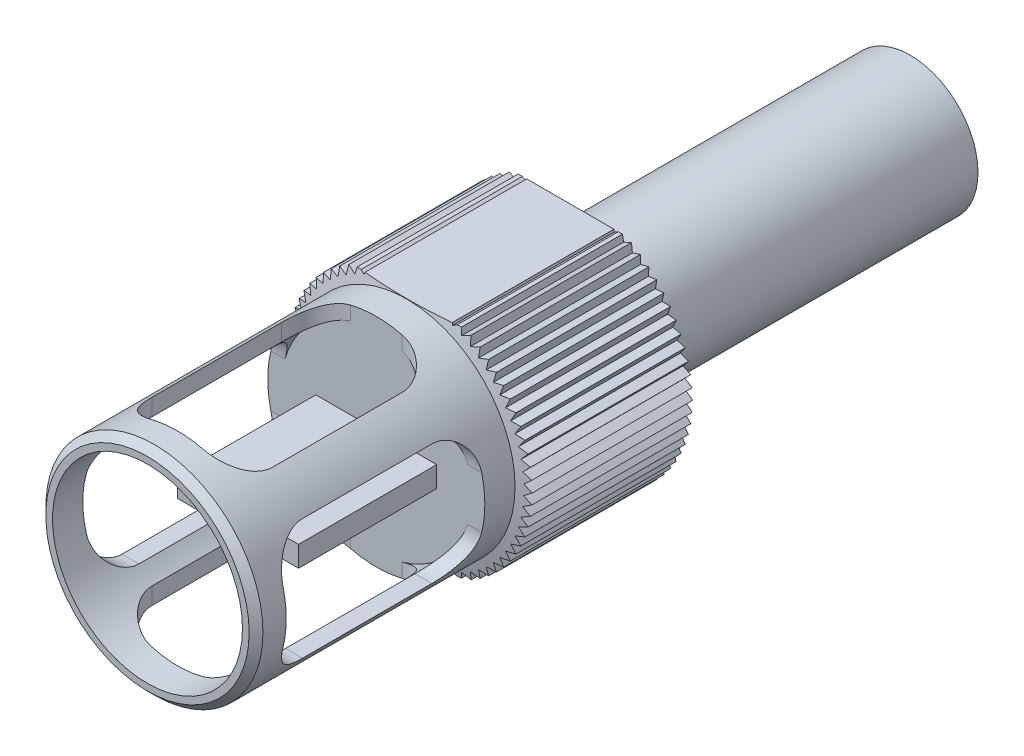
SolidWorks part; units mm, degrees
ref_plane "Front Plane" through (0, 0, 0) normal (0, 0, 1) x (1, 0, 0)
ref_plane "Top Plane" through (0, 0, 0) normal (0, 1, 0) x (1, 0, 0)
ref_plane "Right Plane" through (0, 0, 0) normal (1, 0, 0) x (0, 0, -1)
sketch "Sketch2" plane through (0, 0, 0) normal (1, 0, 0) x (0, 0, -1)
  line L0 (0, 0) -> (0, 7.476)
  line L1 (0, 7.476) -> (0.508, 7.984)
  line L2 (0.508, 7.984) -> (19.05, 7.984)
  line L3 (19.05, 7.984) -> (19.304, 9)
  line L4 (19.304, 9) -> (31.1, 9)
  line L5 (31.1, 9) -> (31.1, 4.984)
  line L6 (31.1, 4.984) -> (56.1, 4.984)
  line L7 (56.1, 4.984) -> (56.1, 0)
  line L8 (0, 0) -> (56.1, 0) construction
  line L9 (0, 0) -> (56.1, 0)
  dimension "D1" = 56.1
  dimension "D2" = 25
  dimension "D3" = 18
  dimension "D4" = 9.968
  dimension "D5" = 1.016
  dimension "D6" = 0.254
  dimension "D7" = 19.05
  dimension "D8" = 0.508
  dimension "D9" = 0.508
revolve "Revolve1" add sketch "Sketch2" angle 360 about L8
sketch "Sketch3" plane through (0, 0, -31.1) normal (0, 0, -1) x (-1, 0, 0)
  line L0 (0, 0) -> (0, 9) construction
  line L1 (0, 9) -> (-0.3704, 8.4839)
  line L2 (0, 9) -> (0.3704, 8.4839)
  line L3 (0, 0) -> (0.3704, 8.4839) construction
  line L4 (-0.3704, 8.4839) -> (0, 0) construction
  line L5 (0.7844, 8.9658) -> (0.3704, 8.4839)
  line L6 (0.7844, 8.9658) -> (1.1084, 8.4193)
  line L7 (0, 0) -> (0.3704, 8.4839) construction
  line L8 (0, 0) -> (1.1084, 8.4193) construction
  circle A0 centre (0, 0) radius 8.492
  circle A1 centre (0, 0) radius 9 construction
  circle A2 centre (0, 0) radius 9
  circle M5 centre (0, 0) radius 9
  dimension "D2" = 0.508
  dimension "D1" = 5
  dimension "D4" = 5
  dimension "D3" = 2
extrude "Cut-Extrude1" cut sketch "Sketch3" against normal through all contours L5 L2 M5
pattern_circular "CirPattern1" count 72 over 360 about axis through (0, 0, 0) along (0, 0, 1) of "Cut-Extrude1"
sketch "Sketch4" plane through (0, 0, 0) normal (0, 0, 1) x (1, 0, 0)
  line L0 (-9.8636, 8) -> (9.8636, 8)
  line L1 (0, 0) -> (12.1385, 0) construction
  line L2 (-9.8636, -8) -> (9.8636, -8)
  circle A0 centre (0, 0) radius 12.7
  dimension "D2" = 25.4
  dimension "D1" = 16
extrude "Cut-Extrude2" cut sketch "Sketch4" against normal through all contours L0 A0 | L2 A0
sketch "Sketch5" plane through (0, 0, 0) normal (1, 0, 0) x (0, 0, -1)
  line L0 (0, 0) -> (19.05, 0) construction
  line L1 (0, 7.476) -> (0, -7.476) construction
  line L2 (19.05, 7.984) -> (19.05, -7.984) construction
  line L4 (14.2875, -4.445) -> (4.7625, -4.445)
  line L5 (16.8275, -1.905) -> (16.8275, 1.905)
  line L6 (14.2875, 4.445) -> (4.7625, 4.445)
  line L7 (2.2225, -1.905) -> (2.2225, 1.905)
  line L8 (16.8275, -4.445) -> (2.2225, 4.445) construction
  line L9 (16.8275, 4.445) -> (2.2225, -4.445) construction
  arc A0 (4.7625, -4.445) -> (2.2225, -1.905) centre (4.7625, -1.905) cw
  arc A1 (14.2875, -4.445) -> (16.8275, -1.905) centre (14.2875, -1.905) ccw
  arc A2 (16.8275, 1.905) -> (14.2875, 4.445) centre (14.2875, 1.905) ccw
  arc A3 (4.7625, 4.445) -> (2.2225, 1.905) centre (4.7625, 1.905) ccw
  point P6 (9.525, 0)
  dimension "D1" = 2.54
  dimension "D2" = 14.605
  dimension "D3" = 8.89
extrude "Cut-Extrude3" cut sketch "Sketch5" against normal through all both and the other way through all
pattern_circular "CirPattern3" count 3 over 180 about axis through (0, 0, 0) along (0, 0, 1) of "Cut-Extrude3"
sketch "Sketch6" plane through (0, 0, 0) normal (0, 0, 1) x (1, 0, 0)
  circle A0 centre (0, 0) radius 6.985
  dimension "D1" = 13.97
extrude "Cut-Extrude4" cut sketch "Sketch6" against normal up to surface (16.8275 mm away) up to face at (0, 0, -16.8275)
sketch "Sketch7" plane through (0, 0, -16.8275) normal (0, 0, 1) x (1, 0, 0)
  line L1 (4.445, -0.762) -> (-4.445, -0.762)
  line L2 (4.445, -0.762) -> (4.445, 0.762)
  line L3 (4.445, 0.762) -> (-4.445, 0.762)
  line L4 (-4.445, -0.762) -> (-4.445, 0.762)
  line L5 (4.445, -0.762) -> (-4.445, 0.762) construction
  line L6 (4.445, 0.762) -> (-4.445, -0.762) construction
  point P0 (0, 0)
  dimension "D1" = 1.524
  dimension "D2" = 8.89
extrude "Boss-Extrude1" add sketch "Sketch7" along normal blind 10.16
